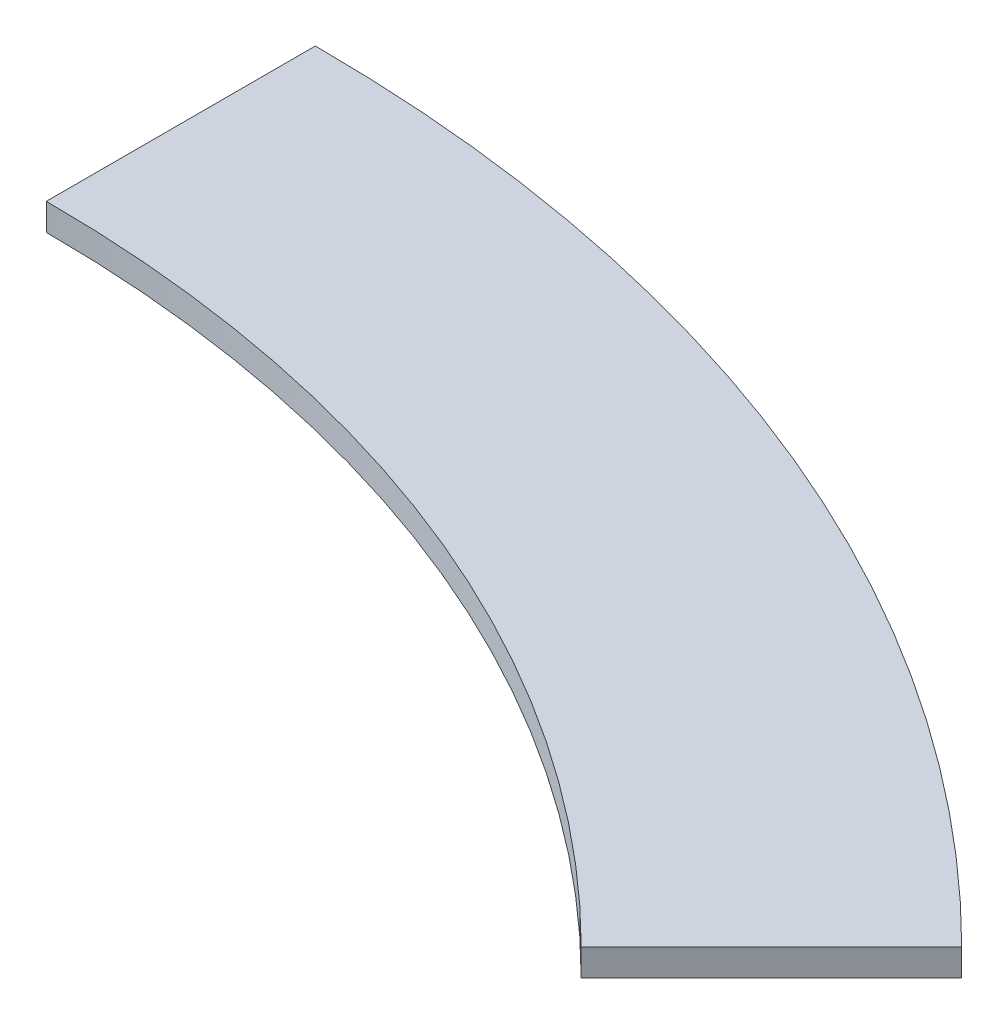
SolidWorks part; units mm, degrees
ref_plane "Front Plane" through (0, 0, 0) normal (0, 0, 1) x (1, 0, 0)
ref_plane "Top Plane" through (0, 0, 0) normal (0, 1, 0) x (1, 0, 0)
ref_plane "Right Plane" through (0, 0, 0) normal (1, 0, 0) x (0, 0, -1)
sketch "Sketch1" plane through (0, 0, 0) normal (0, 1, 0) x (1, 0, 0)
  line L0 (0, 0) -> (0, 480) construction
  line L1 (0, 480) -> (0, 580)
  line L2 (0, 0) -> (410.1219, 410.1219) construction
  line L3 (339.4113, 339.4113) -> (410.1219, 410.1219)
  arc A0 (0, 480) -> (339.4113, 339.4113) centre (0, 0) cw
  arc A1 (0, 580) -> (410.1219, 410.1219) centre (0, 0) cw
  dimension "D1" = 480
  dimension "D2" = 100
  dimension "D3" = 580
  dimension "D4" = 45
extrude "Boss-Extrude1" add sketch "Sketch1" along normal blind 10 contours A1 L1 A0 L3
